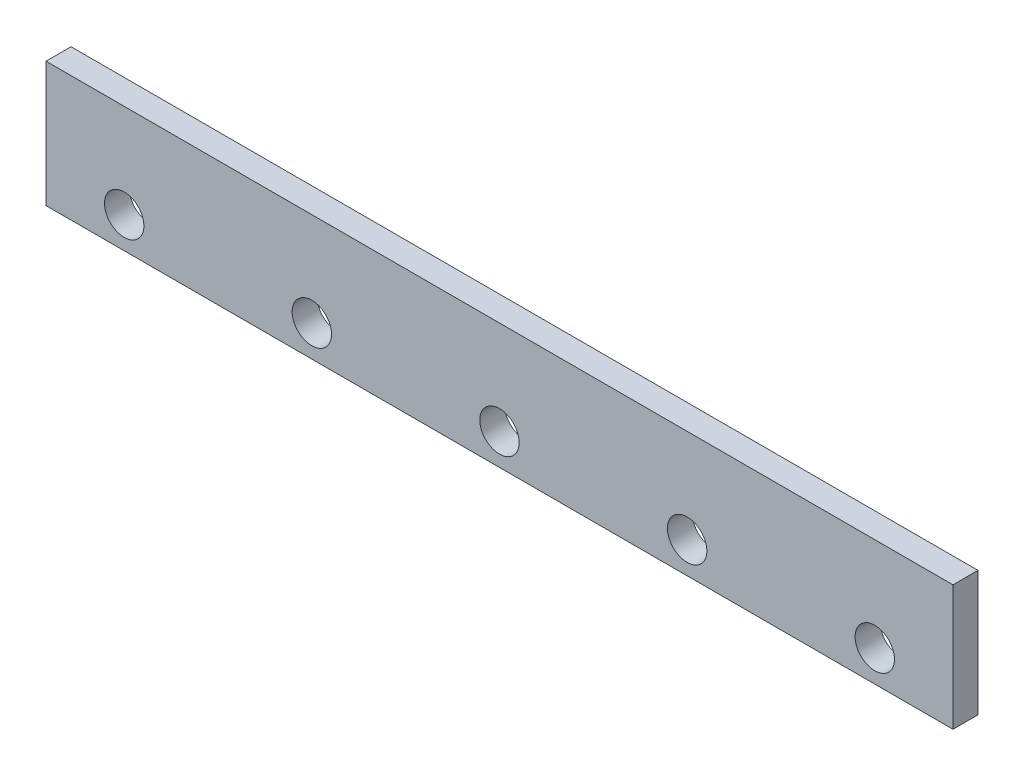
SolidWorks part; units mm, degrees
ref_plane "Front Plane" through (0, 0, 0) normal (0, 0, 1) x (1, 0, 0)
ref_plane "Top Plane" through (0, 0, 0) normal (0, 1, 0) x (1, 0, 0)
ref_plane "Right Plane" through (0, 0, 0) normal (1, 0, 0) x (0, 0, -1)
sketch "Sketch1" plane through (0, 0, 0) normal (0, 0, 1) x (1, 0, 0)
  line L1 (0, 0) -> (580, 0)
  line L2 (0, 0) -> (0, 80)
  line L3 (0, 80) -> (580, 80)
  line L4 (580, 0) -> (580, 80)
  dimension "D1" = 580
  dimension "D2" = 80
extrude "Boss-Extrude1" add sketch "Sketch1" along normal blind 16
sketch "Sketch2" plane through (0, 0, 16) normal (0, 0, 1) x (1, 0, 0)
  line L0 (0, 80) -> (0, 0) construction
  line L2 (0, 0) -> (580, 0) construction
  line L3 (580, 80) -> (0, 80) construction
  circle A0 centre (50, 20) radius 12.6
  circle A1 centre (170, 20) radius 12.6
  circle A2 centre (290, 20) radius 12.6
  circle A3 centre (410, 20) radius 12.6
  circle A4 centre (530, 20) radius 12.6
  dimension "D4" = 25.2
  dimension "D1" = 50
  dimension "D5" = 20
  dimension "D6" = 120
  dimension "D7" = 60
  dimension "D2" = 5
extrude "Cut-Extrude1" cut sketch "Sketch2" against normal blind 16
